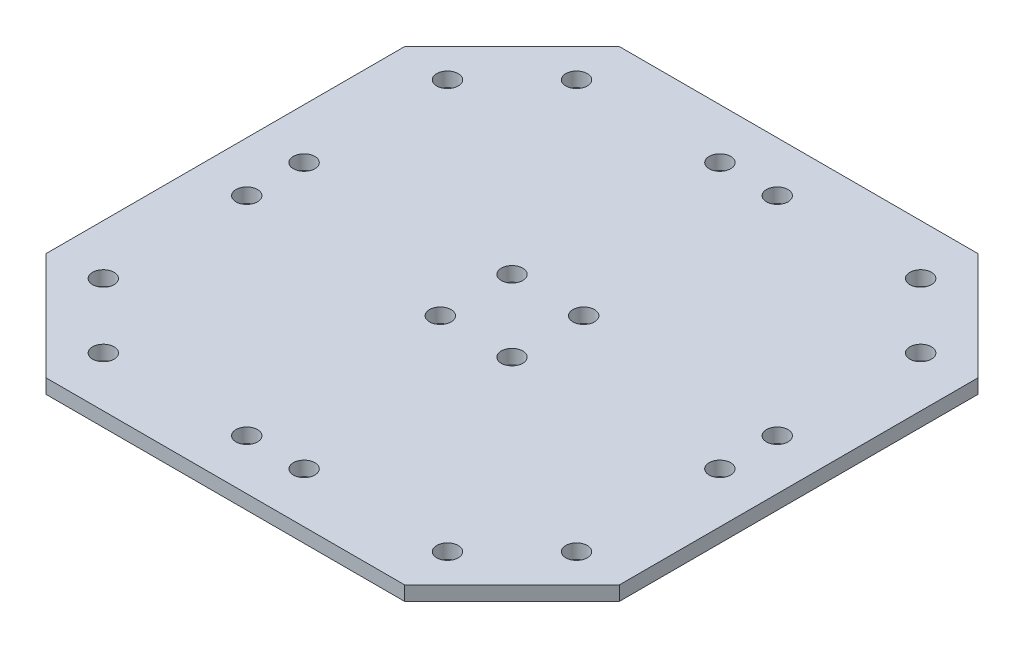
SolidWorks part; units mm, degrees
ref_plane "Front Plane" through (0, 0, 0) normal (0, 0, 1) x (1, 0, 0)
ref_plane "Top Plane" through (0, 0, 0) normal (0, 1, 0) x (1, 0, 0)
ref_plane "Right Plane" through (0, 0, 0) normal (1, 0, 0) x (0, 0, -1)
sketch "Sketch1" plane through (0, 0, 0) normal (0, 1, 0) x (1, 0, 0)
  line L1 (0, 0) -> (40, 0)
  line L2 (0, 0) -> (0, 40)
  line L3 (0, 40) -> (25, 40)
  line L4 (40, 0) -> (40, 25)
  line L7 (25, 40) -> (40, 25)
  arc A3 (71.9645, 86.9645) -> (79.0355, 86.9645) centre (75.5, 83.4289) cw
  dimension "D1" = 40
  dimension "D2" = 40
  dimension "D3" = 25
  dimension "D4" = 25
extrude "Boss-Extrude1" add sketch "Sketch1" along normal blind 2 contours L7 L3 L2 L1 L4
sketch "Sketch6" plane through (0, 3, 0) normal (0, 1, 0) x (1, 0, 0)
  line L0 (33, 4) -> (33, 24) construction
  line L1 (33, 24) -> (24, 33) construction
  line L2 (24, 33) -> (4, 33) construction
  line L7 (0, 0) -> (40, 0) construction
  line L9 (0, 0) -> (0, 40) construction
  circle A0 centre (33, 24) radius 1.5
  circle A1 centre (24, 33) radius 1.5
  circle A2 centre (4, 33) radius 1.5
  circle A3 centre (33, 4) radius 1.5
  circle A4 centre (5, 5) radius 1.5
  dimension "D1" = 5
  dimension "D7" = 4
  dimension "D2" = 5
  dimension "D3" = 12.7279
  dimension "D4" = 20
  dimension "D5" = 20
  dimension "D6" = 4
extrude "Cut-Extrude3" cut sketch "Sketch6" against normal through all
mirror "Mirror2" about plane through (0, 0, 0) normal (1, 0, 0) of "Boss-Extrude1", "Cut-Extrude3"
